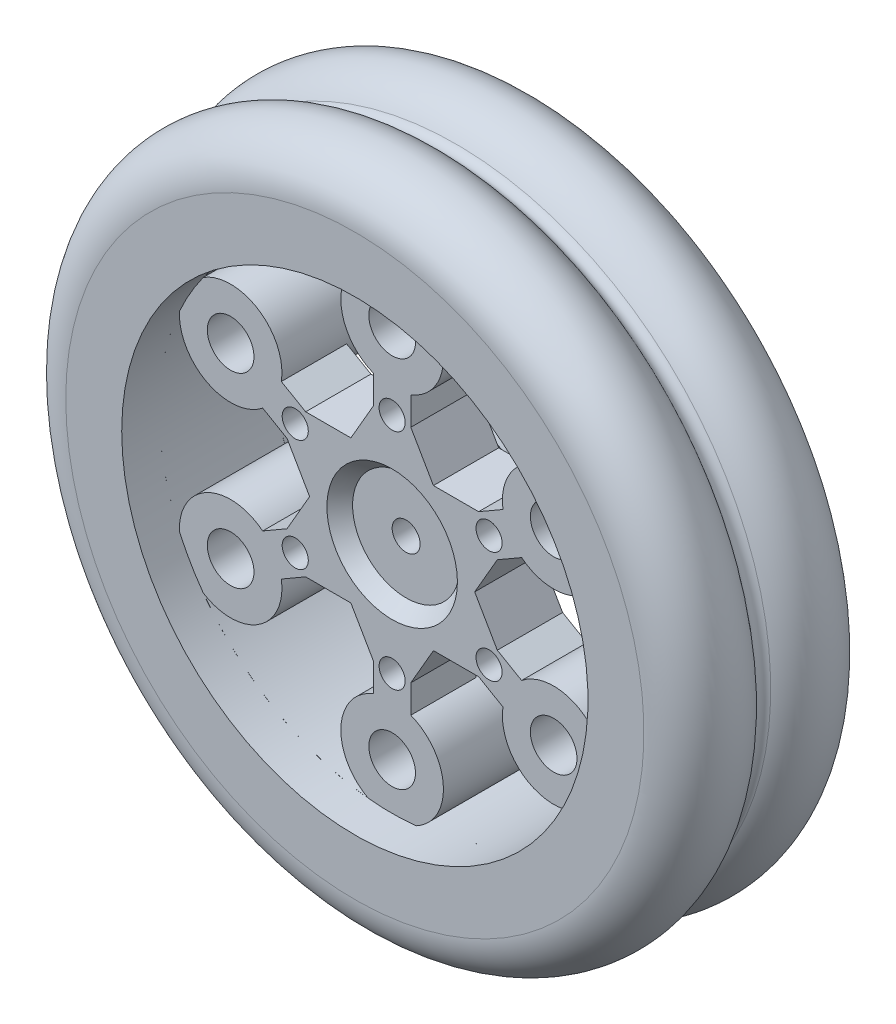
SolidWorks part; units mm, degrees
material "尼龙 6/10"
ref_plane "前视基准面" through (0, 0, 0) normal (0, 0, 1) x (1, 0, 0)
ref_plane "上视基准面" through (0, 0, 0) normal (0, 1, 0) x (1, 0, 0)
ref_plane "右视基准面" through (0, 0, 0) normal (1, 0, 0) x (0, 0, -1)
sketch "草图1" plane through (0, 0, 0) normal (0, 1, 0) x (1, 0, 0)
  line L0 (25, 10) -> (25, -10)
  line L1 (0, 146.934) -> (0, -105.6267) construction
  line L2 (25, 10) -> (31, 10)
  line L3 (25, -10) -> (31, -10)
  line L4 (-236.5493, 0) -> (326.6118, 0) construction
  arc A0 (33.7639, 0.8333) -> (31, 10) centre (31, 5) ccw
  arc A1 (33.7639, 0.8333) -> (33.7639, -0.8333) centre (34.3166, 0) ccw
  arc A2 (31, -10) -> (33.7639, -0.8333) centre (31, -5) ccw
  point P15 (31, 0)
  dimension "D4" = 1
  dimension "D1" = 20
  dimension "D2" = 25
  dimension "D3" = 31
revolve "旋转1" add sketch "草图1" angle 360 about L1
ref_plane "基准面1" through (0, 0, 6) normal (0, 0, 1) x (1, 0, 0)
sketch "草图2" plane through (0, 0, 6) normal (0, 0, 1) x (1, 0, 0)
  line L0 (0, 38.7462) -> (0, -39.0495) construction
  circle A0 centre (0, 0) radius 20 construction
  circle A1 centre (0, 20) radius 5.5
  dimension "D1" = 40
  dimension "D2" = 11
extrude "凸台-拉伸1" add sketch "草图2" against normal blind 10
pattern_circular "阵列(圆周)1" count 6 over 360 about axis through (0, 0, 0) along (0, 0, 1) of "凸台-拉伸1"
sketch "草图3" plane through (0, 0, 6) normal (0, 0, 1) x (1, 0, 0)
  line L0 (-8.8498, 0) -> (-11.2748, -4.2001)
  line L1 (0, 16) -> (-13.8564, 8) construction
  line L2 (-13.8564, 8) -> (-13.8564, -8) construction
  line L3 (-13.8564, -8) -> (0, -16) construction
  line L4 (0, -16) -> (13.8564, -8) construction
  line L5 (13.8564, -8) -> (13.8564, 8) construction
  line L6 (13.8564, 8) -> (0, 16) construction
  line L7 (-9.2748, -7.6642) -> (-4.4249, -7.6642)
  line L8 (11.2748, -4.2001) -> (8.8498, 0)
  line L9 (9.2748, 7.6642) -> (4.4249, 7.6642)
  line L10 (-11.2748, 4.2001) -> (-8.8498, 0)
  line L11 (-4.4249, -7.6642) -> (-2, -11.8643)
  line L12 (0, 43.2923) -> (0, -38.3052) construction
  line L13 (-2, 14.8765) -> (-2, 11.8643)
  line L14 (2, 11.8643) -> (2, 14.8765)
  line L15 (11.2748, 4.2001) -> (13.8834, 5.7062)
  line L16 (11.8834, 9.1703) -> (9.2748, 7.6642)
  line L17 (9.2748, -7.6642) -> (11.8834, -9.1703)
  line L18 (13.8834, -5.7062) -> (11.2748, -4.2001)
  line L19 (-2, -11.8643) -> (-2, -14.8765)
  line L20 (2, -14.8765) -> (2, -11.8643)
  line L21 (-11.2748, -4.2001) -> (-13.8834, -5.7062)
  line L22 (-11.8834, -9.1703) -> (-9.2748, -7.6642)
  line L23 (-9.2748, 7.6642) -> (-11.8834, 9.1703)
  line L24 (-13.8834, 5.7062) -> (-11.2748, 4.2001)
  line L25 (-2, 11.8643) -> (-4.4249, 7.6642)
  line L26 (2, -11.8643) -> (4.4249, -7.6642)
  line L27 (4.4249, -7.6642) -> (9.2748, -7.6642)
  line L28 (-4.4249, 7.6642) -> (-9.2748, 7.6642)
  line L29 (4.4249, 7.6642) -> (2, 11.8643)
  line L30 (8.8498, 0) -> (11.2748, 4.2001)
  circle A0 centre (0, 0) radius 13.8564 construction
  arc A1 (-2.5584, 24.8688) -> (2.5584, 24.8688) centre (0, 20) ccw construction
  arc A2 (-2, 14.8765) -> (2, 14.8765) centre (0, 20) ccw
  arc A3 (-22.8162, 10.2188) -> (-20.2578, 14.65) centre (-17.3205, 10) ccw construction
  arc A4 (-20.2578, -14.65) -> (-22.8162, -10.2188) centre (-17.3205, -10) ccw construction
  arc A5 (2.5584, -24.8688) -> (-2.5584, -24.8688) centre (0, -20) ccw construction
  arc A6 (22.8162, -10.2188) -> (20.2578, -14.65) centre (17.3205, -10) ccw construction
  arc A7 (20.2578, 14.65) -> (22.8162, 10.2188) centre (17.3205, 10) ccw construction
  arc A8 (-13.8834, 5.7062) -> (-11.8834, 9.1703) centre (-17.3205, 10) ccw
  arc A9 (-11.8834, -9.1703) -> (-13.8834, -5.7062) centre (-17.3205, -10) ccw
  arc A10 (2, -14.8765) -> (-2, -14.8765) centre (0, -20) ccw
  arc A11 (13.8834, -5.7062) -> (11.8834, -9.1703) centre (17.3205, -10) ccw
  arc A12 (11.8834, 9.1703) -> (13.8834, 5.7062) centre (17.3205, 10) ccw
  point P41 (0, 0)
  dimension "D1" = 32
  dimension "D2" = 4
  dimension "D3" = 6
extrude "凸台-拉伸2" add sketch "草图3" against normal blind 7
sketch "草图4" plane through (0, 0, -1) normal (0, 0, -1) x (-1, 0, 0)
  line L0 (0, 15.11) -> (0, -12.4392) construction
  circle A0 centre (0, 0) radius 12 construction
  circle A1 centre (0, 12) radius 1.4
  dimension "D1" = 24
  dimension "D2" = 2.8
extrude "切除-拉伸1" cut sketch "草图4" against normal through all
pattern_circular "阵列(圆周)2" count 6 over 360 about axis through (0, 0, 0) along (0, 0, 1) of "切除-拉伸1"
sketch "草图5" plane through (0, 0, -1) normal (0, 0, -1) x (-1, 0, 0)
  circle A0 centre (0, 0) radius 9
  dimension "D1" = 18
extrude "凸台-拉伸3" add sketch "草图5" along normal blind 5
sketch "草图7" plane through (0, 0, 6) normal (0, 0, 1) x (1, 0, 0)
  circle A0 centre (0, 0) radius 7
  dimension "D1" = 14
extrude "切除-拉伸3" cut sketch "草图7" against normal blind 1.5 draft 40
sketch "草图8" plane through (0, 0, 4.5) normal (0, 0, 1) x (1, 0, 0)
  circle A0 centre (0, 0) radius 1.5
  dimension "D1" = 3
extrude "切除-拉伸4" cut sketch "草图8" against normal through all
sketch "草图10" plane through (0, 0, 6) normal (0, 0, 1) x (1, 0, 0)
  circle A0 centre (0, 20) radius 1.25
  dimension "D1" = 2.5
extrude "切除-拉伸6" cut sketch "草图10" against normal through all
sketch "草图11" plane through (0, 0, 6) normal (0, 0, 1) x (1, 0, 0)
  circle A0 centre (0, 20) radius 2.5
  dimension "D1" = 5
extrude "切除-拉伸7" cut sketch "草图11" against normal through all
pattern_circular "阵列(圆周)4" count 6 over 360 about axis through (0, 0, 0) along (0, 0, 1) of "切除-拉伸7"
sketch "草图13" plane through (0, 0, 0) normal (0, 1, 0) x (1, 0, 0)
  line L0 (0, 19.3352) -> (0, -18.3764) construction
  line L1 (21, 6) -> (26, 6)
  line L2 (26, 6) -> (26, -6)
  line L3 (26, -6) -> (21, -6)
  line L4 (-6.1819, 0) -> (35.4823, 0) construction
  dimension "D1" = 26
  dimension "D2" = 12
  dimension "D3" = 5
surface "曲面-旋转1" sketch "草图13" parameters "D1"=360
surface "曲面-剪裁2"
sketch "草图14" plane through (0, 0, -6) normal (0, 0, -1) x (-1, 0, 0)
  line L0 (0, 12) -> (0, 0) construction
  line L2 (0, 6.9282) -> (-6, 3.4641)
  line L3 (-6, 3.4641) -> (-6, -3.4641)
  line L4 (-6, -3.4641) -> (0, -6.9282)
  line L5 (0, -6.9282) -> (6, -3.4641)
  line L6 (6, -3.4641) -> (6, 3.4641)
  line L7 (6, 3.4641) -> (0, 6.9282)
  circle A0 centre (0, 0) radius 6 construction
  dimension "D1" = 12
extrude "切除-拉伸9" cut sketch "草图14" against normal blind 8
